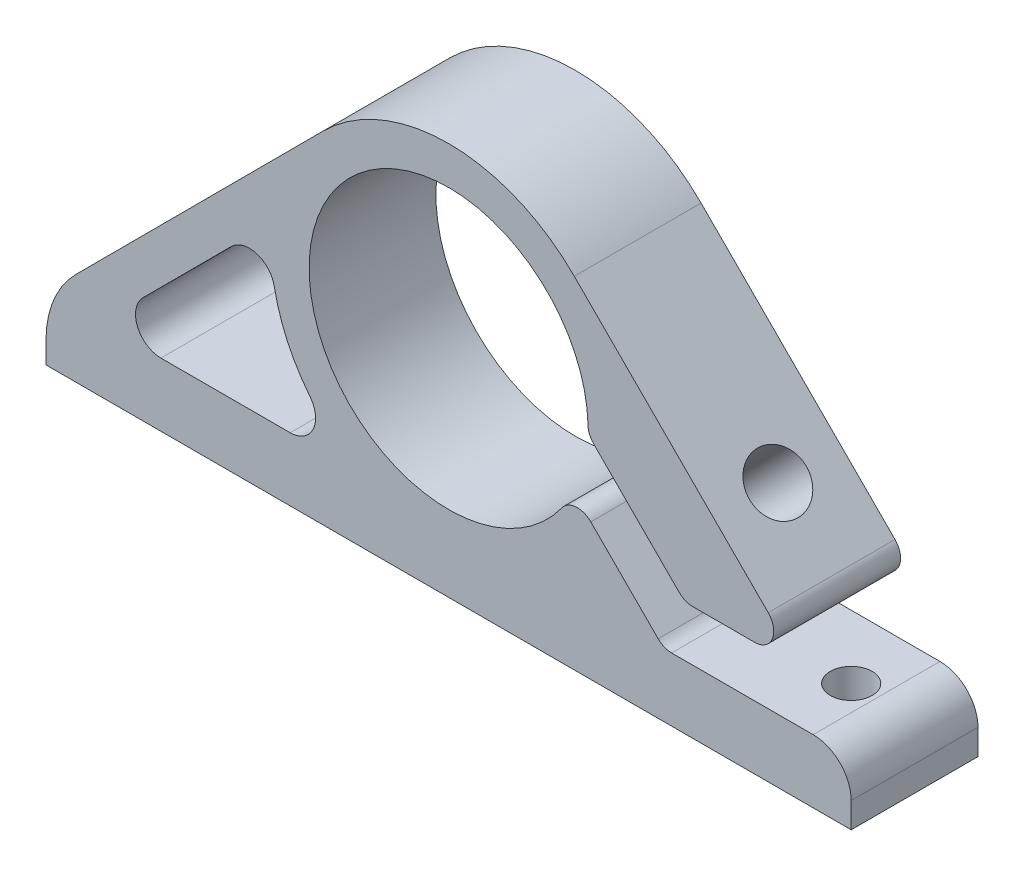
SolidWorks part; units mm, degrees
material "Сплав 2024"
ref_plane "Спереди" through (0, 0, 0) normal (0, 0, 1) x (1, 0, 0)
ref_plane "Сверху" through (0, 0, 0) normal (0, 1, 0) x (1, 0, 0)
ref_plane "Справа" through (0, 0, 0) normal (1, 0, 0) x (0, 0, -1)
sketch "Эскиз1" plane through (0, 0, 0) normal (0, 0, 1) x (1, 0, 0)
  line L0 (0, 32.0117) -> (0, -47.9255) construction
  line L1 (-31.75, -12) -> (-9.9106, 9.8884)
  line L3 (-31.75, -12) -> (-31.75, -17)
  line L4 (-31.75, -17) -> (31.75, -17)
  line L5 (31.75, -12) -> (31.75, -17)
  line L6 (-31.75, -12) -> (31.75, -17) construction
  line L7 (-31.75, -17) -> (31.75, -12) construction
  line L8 (31.75, -12) -> (9.9106, 9.8884)
  circle A0 centre (0, 0) radius 11
  arc A1 (9.9106, 9.8884) -> (-9.9106, 9.8884) centre (0, 0) ccw
  circle A3 centre (0, 0) radius 14 construction
  point P5 (0, -14.5)
  point P12 (14, 0)
  dimension "D1" = 22
  dimension "D5" = 14.5
  dimension "D3" = 5
  dimension "D4" = 63.5
  dimension "D6" = 5
  dimension "D2" = 3
extrude "Бобышка-Вытянуть1" add sketch "Эскиз1" along normal blind 10
sketch "Эскиз2" plane through (0, 0, 10) normal (0, 0, 1) x (1, 0, 0)
  line L1 (10.9943, -0.3532) -> (18.624, -8)
  line L2 (10.9943, -0.3532) -> (9.859, -4.8785)
  line L3 (9.859, -4.8785) -> (16.9645, -12)
  line L6 (31.75, -12) -> (9.9106, 9.8884) construction
  line L7 (31.75, -12) -> (-31.75, -12) construction
  line L9 (31.75, -12) -> (16.9645, -12)
  line L10 (31.75, -12) -> (31.75, -8)
  line L11 (31.75, -8) -> (18.624, -8)
  circle A0 centre (0, 0) radius 11 construction
  dimension "D1" = 4
  dimension "D3" = 4
extrude "Вырез-Вытянуть1" cut sketch "Эскиз2" against normal through all
fillet "Скругление1" radius 1.5 5 edges at (16.9645, -12, 5) (18.624, -8, 5) (27.759, -8, 5) (9.859, -4.8785, 5) (10.9943, -0.3532, 5)
sketch "Эскиз3" plane through (0, -17, 0) normal (0, -1, 0) x (1, 0, 0)
  line L0 (-31.75, 5) -> (31.75, 5) construction
  line L1 (-31.75, 10) -> (-31.75, 0) construction
  line L2 (31.75, 10) -> (31.75, 0) construction
  line L3 (-26.75, 10) -> (-26.75, 0) construction
  line L4 (-31.75, 10) -> (31.75, 10) construction
  line L5 (-31.75, 0) -> (31.75, 0) construction
  line L6 (26.75, 10) -> (26.75, 0) construction
  dimension "D1" = 5
  dimension "D2" = 5
hole_wizard "Отверстие обработанное метчиком M4x0.71" positions "Эскиз5" profile "Эскиз4" tap size "M4x0.7" standard "Ansi Metric"
sketch "Эскиз5" plane through (0, -17, 0) normal (0, -1, 0) x (-1, 0, 0)
  line L0 (31.75, -5) -> (-31.75, -5) construction
  line L1 (26.75, -10) -> (26.75, 0) construction
  line L2 (-26.75, -10) -> (-26.75, 0) construction
  point P0 (26.75, -5)
  point P2 (-26.75, -5)
sketch "Эскиз4" plane through (-26.75, -17, 5) normal (1, 0, 0) x (0, 0, -1)
  line L0 (0, 0) -> (0, 5.9914)
  line L1 (0, 5.9914) -> (1.65, 5)
  line L2 (1.65, 5) -> (1.65, 0)
  line L5 (1.65, 0) -> (0, 0)
  line L10 (0, 5.9914) -> (-1.65, 5) construction
  line L11 (0, -6.35) -> (0, 107.95) construction
  dimension "Диаметр сверла" = 3.3
  dimension "Глубина сверла" = 5
  dimension "Угол заточки сверла" = 118
cosmetic thread "Отверстие резьбы1" parameters "D1"=5, "D2"=4
cosmetic thread "Отверстие резьбы2" parameters "D1"=5, "D2"=4
sketch "Эскиз6" plane through (9.9106, 9.8884, 0) normal (0.7079, 0.7063, 0) x (0, 0, -1)
  line L0 (-5, -21.6541) -> (-5, 0) construction
  line L1 (-10, -21.6541) -> (0, -21.6541) construction
  line L2 (-10, 0) -> (0, 0) construction
  line L3 (-10, -15.6541) -> (0, -15.6541) construction
  line L4 (-10, -21.6541) -> (-10, 0) construction
  line L5 (0, -21.6541) -> (0, 0) construction
  dimension "D1" = 6
hole_wizard "Отверстие с зазором M41" positions "Эскиз8" profile "Эскиз7" hole size "M4" standard "Ansi Metric" end condition up to next
sketch "Эскиз8" plane through (9.9106, 9.8884, 0) normal (0.7079, 0.7063, 0) x (0, 0, -1)
  line L0 (-5, -21.6541) -> (-5, 0) construction
  line L1 (-10, -15.6541) -> (0, -15.6541) construction
  point P0 (-5, -15.6541)
sketch "Эскиз7" plane through (20.9673, -1.1931, 5) normal (0, 0, 1) x (-0.7063, 0.7079, 0)
  line L0 (0, 0) -> (0, 6.4666)
  line L1 (0, 6.4666) -> (2.25, 6.4666)
  line L2 (2.25, 6.4666) -> (2.25, 0)
  line L5 (2.25, 0) -> (0, 0)
  line L11 (0, -6.35) -> (0, 107.95) construction
  dimension "Диаметр сквозного отверстия" = 4.5
  dimension "Глубина сквозного отверстия" = 6.4666
hole_wizard "Отверстие обработанное метчиком M4x0.72" positions "Эскиз10" profile "Эскиз9" tap size "M4x0.7" standard "Ansi Metric" end condition through all
sketch "Эскиз10" plane through (2.5013, 2.4957, 0) normal (0.7079, 0.7063, 0) x (0, 0, -1)
  line L0 (-5, -21.6541) -> (-5, 0) construction
  line L1 (-10, -15.6541) -> (0, -15.6541) construction
  point P0 (-5, -15.6541)
cosmetic thread "Отверстие резьбы3" parameters "D2"=4
sketch "Эскиз9" plane through (13.558, -8.5859, 5) normal (0, 0, 1) x (-0.7063, 0.7079, 0)
  line L0 (0, 0) -> (0, 38.0165)
  line L1 (0, 38.0165) -> (1.65, 38.0165)
  line L2 (1.65, 38.0165) -> (1.65, 0)
  line L5 (1.65, 0) -> (0, 0)
  line L11 (0, -6.35) -> (0, 107.95) construction
  dimension "Диаметр проходного сверла" = 3.3
  dimension "Глубина проходного сверла" = 38.0165
fillet "Скругление2" radius 3 1 edges at (31.75, -12, 5)
sketch "Эскиз11" plane through (0, 0, 10) normal (0, 0, 1) x (1, 0, 0)
  line L0 (-13.9037, 1.6389) -> (-24.1071, -8.5874)
  line L1 (-22.6913, -12) -> (-7.2111, -12)
  line L2 (-31.75, -17) -> (31.75, -17) construction
  line L3 (-9.9106, 9.8884) -> (-31.75, -12) construction
  arc A0 (-24.1071, -8.5874) -> (-22.6913, -12) centre (-22.6913, -10) ccw
  arc A1 (-13.9037, 1.6389) -> (-7.2111, -12) centre (0, 0) ccw
  dimension "D3" = 4
  dimension "D4" = 14
  dimension "D1" = 5
  dimension "D2" = 3
extrude "Вырез-Вытянуть2" cut sketch "Эскиз11" against normal through all
fillet "Скругление3" radius 2 2 edges at (-7.2111, -12, 5) (-13.9037, 1.6389, 5)
fillet "Скругление5" radius 8 1 edges at (-31.75, -12, 5)
